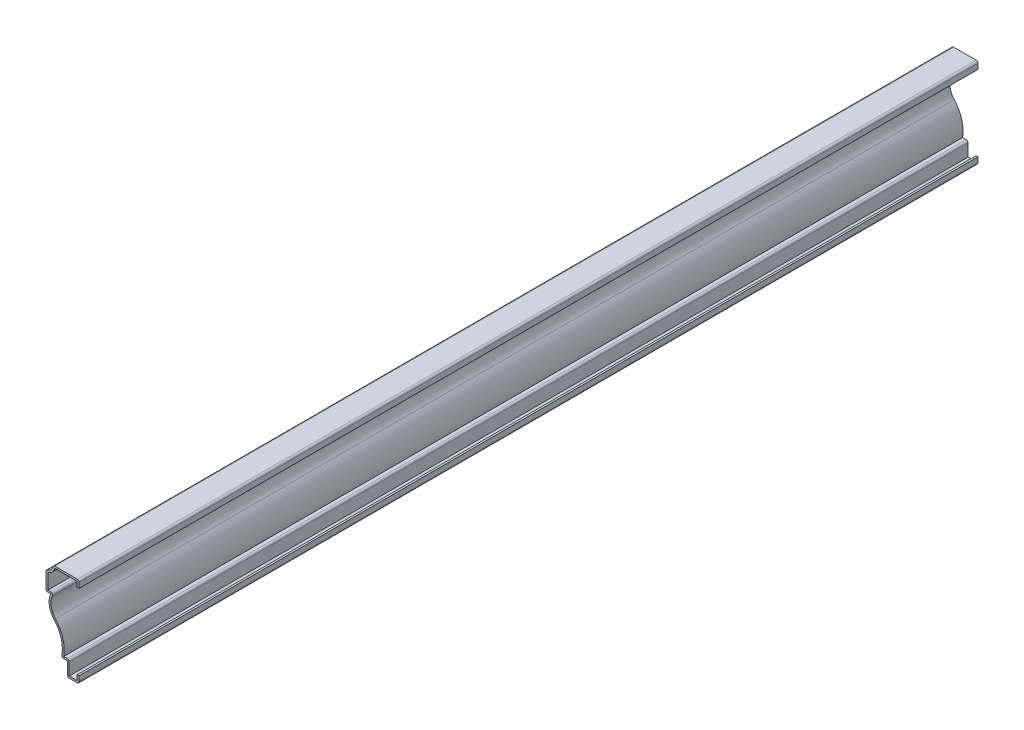
SolidWorks part; units mm, degrees
ref_plane "Front Plane" through (0, 0, 0) normal (0, 0, 1) x (1, 0, 0)
ref_plane "Top Plane" through (0, 0, 0) normal (0, 1, 0) x (1, 0, 0)
ref_plane "Right Plane" through (0, 0, 0) normal (1, 0, 0) x (0, 0, -1)
sketch "Sketch1" plane through (0, 0, 0) normal (0, 0, 1) x (1, 0, 0)
  line L0 (0, 0) -> (0, 60.325) construction
  line L1 (0, 55.5625) -> (0, 60.325)
  line L2 (0, 60.325) -> (-17.4625, 60.325)
  line L3 (-22.225, 55.5625) -> (-22.225, 42.7953)
  line L4 (-22.225, 42.7953) -> (-19.05, 42.7953)
  line L5 (-11.9063, 9.525) -> (-7.9375, 9.525)
  line L6 (-7.9375, 9.525) -> (-7.9375, 0)
  line L7 (-7.9375, 0) -> (0, 0)
  line L8 (0, 0) -> (0, 4.7625)
  arc A0 (-17.4625, 60.325) -> (-22.225, 55.5625) centre (-22.225, 60.325) cw
  arc A1 (-19.05, 42.7953) -> (-16.845, 29.0958) centre (-7.4452, 37.636) ccw
  arc A2 (-16.845, 29.0958) -> (-11.9063, 9.525) centre (-32.7072, 14.6844) cw
  point P16 (0, 64.4363)
  dimension "D9" = 21.4312
  dimension "D10" = 12.7
  dimension "D14" = 4.7625
  dimension "D1" = 4.7625
  dimension "D2" = 4.7625
  dimension "D3" = 60.325
  dimension "D4" = 22.225
  dimension "D5" = 7.9375
  dimension "D6" = 3.9688
  dimension "D7" = 9.525
  dimension "D8" = 10.3187
  dimension "D11" = 5.1594
  dimension "D12" = 5.1594
  dimension "D13" = 3.175
extrude "Extrude-Thin1" add sketch "Sketch1" against normal blind 603.25 thin thin type one direction reverse wall 1.27
fillet "Fillet1" radius 1.27 9 edges at (0, 0, -301.625) (-7.9375, 0, -301.625) (-6.6675, 10.795, -301.625) (-11.9062, 9.525, -301.625) (-16.8955, 44.0653, -301.625) (-22.225, 42.7953, -301.625) (-22.225, 55.5625, -301.625) (-17.4625, 60.325, -301.625) (0, 60.325, -301.625)
